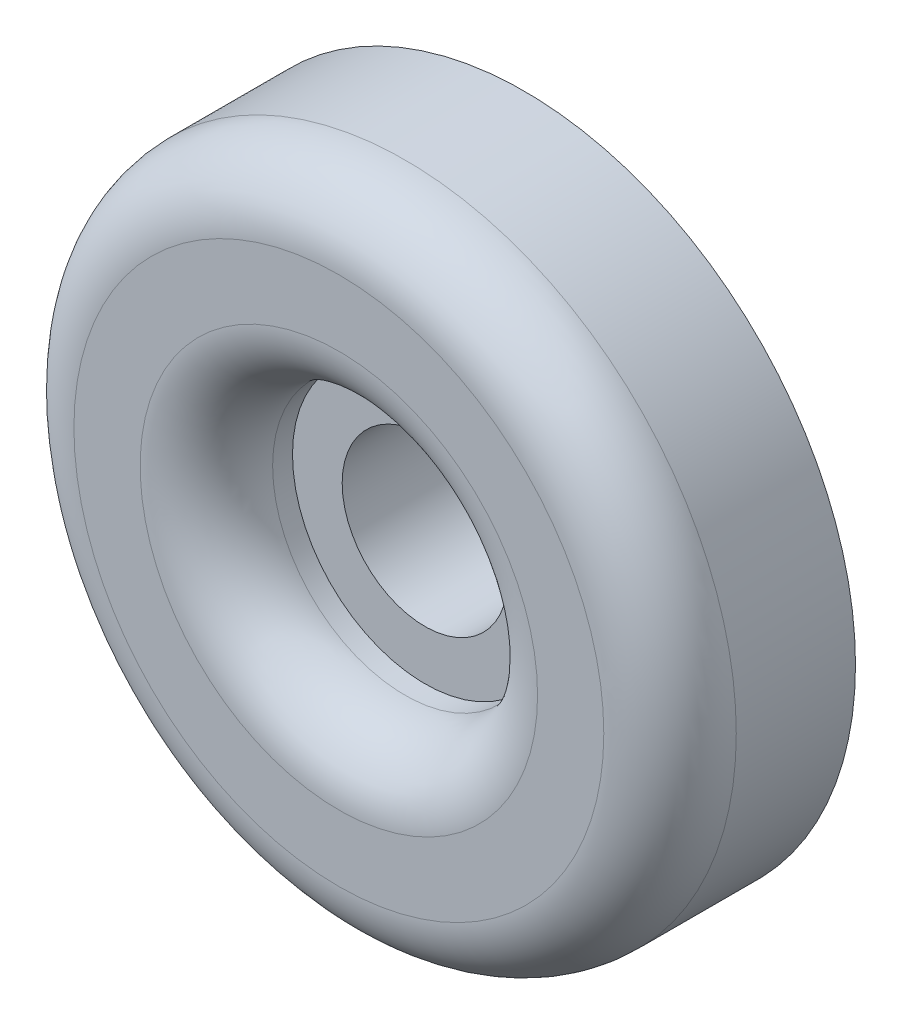
SolidWorks part; units mm, degrees
ref_plane "Front Plane" through (0, 0, 0) normal (1, 0, 0) x (0, 1, 0)
ref_plane "Top Plane" through (0, 0, 0) normal (0, 0, 1) x (0, 1, 0)
ref_plane "Right Plane" through (0, 0, 0) normal (0, 1, 0) x (-1, 0, 0)
sketch "Sketch1" plane through (0, 0, 0) normal (0, 0, 1) x (0, 1, 0)
  circle A0 centre (0, 0) radius 12.7
  circle A1 centre (0, 0) radius 3.175
  dimension "D1" = 25.4
  dimension "D2" = 6.35
extrude "Boss-Extrude1" add sketch "Sketch1" along normal blind 3.81
sketch "Sketch2" plane through (0, 0, 3.81) normal (0, 0, 1) x (1, 0, 0)
  circle A0 centre (0, 0) radius 12.7
  circle A1 centre (0, 0) radius 5.08
  dimension "D1" = 25.4
  dimension "D2" = 10.16
extrude "Boss-Extrude2" add sketch "Sketch2" along normal blind 3.302
fillet "Fillet2" radius 2.54 2 edges at (5.08, 0, 7.112) (12.7, 0, 7.112)
